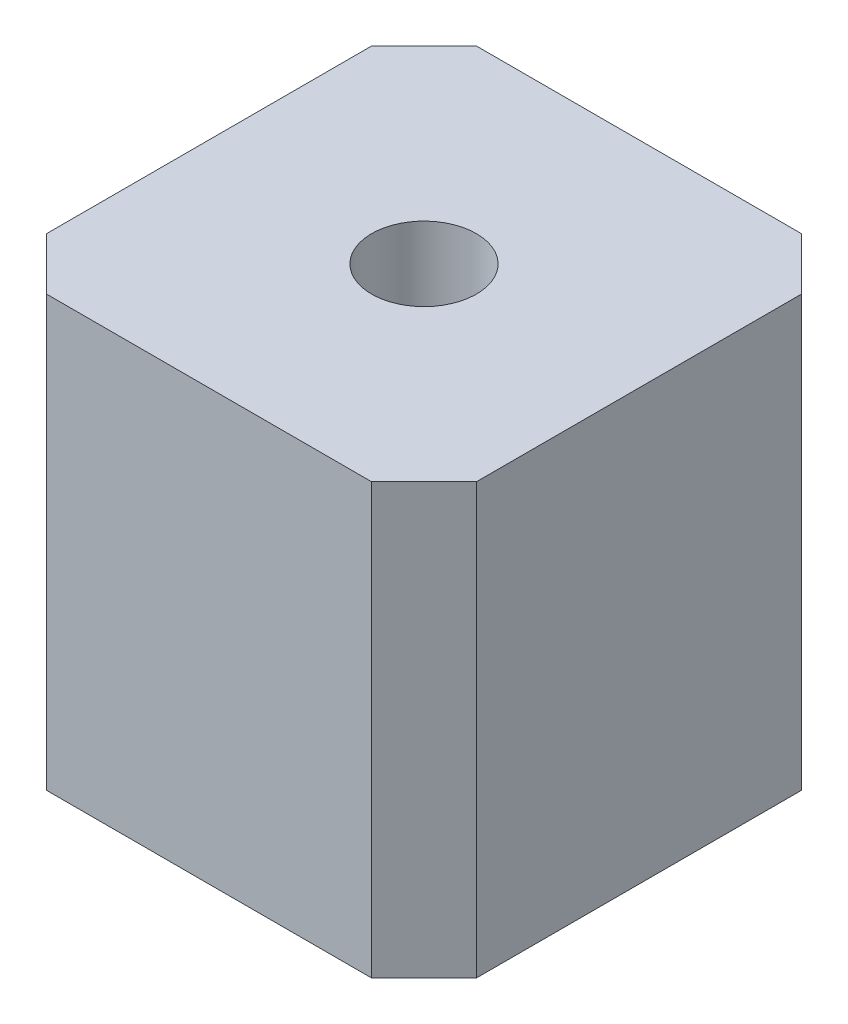
SolidWorks part; units mm, degrees
ref_plane "Front Plane" through (0, 0, 0) normal (0, 0, 1) x (1, 0, 0)
ref_plane "Top Plane" through (0, 0, 0) normal (0, 1, 0) x (1, 0, 0)
ref_plane "Right Plane" through (0, 0, 0) normal (1, 0, 0) x (0, 0, -1)
sketch "Sketch1" plane through (0, 0, 0) normal (0, 1, 0) x (1, 0, 0)
  line L1 (-20.5, -20.5) -> (20.5, -20.5)
  line L2 (-20.5, -20.5) -> (-20.5, 20.5)
  line L3 (-20.5, 20.5) -> (20.5, 20.5)
  line L4 (20.5, -20.5) -> (20.5, 20.5)
  line L5 (-20.5, -20.5) -> (20.5, 20.5) construction
  line L6 (-20.5, 20.5) -> (20.5, -20.5) construction
  point P0 (0, 0)
  dimension "D1" = 41
  dimension "D2" = 41
extrude "Boss-Extrude1" add sketch "Sketch1" along normal blind 41
chamfer "Chamfer1" distance 5 angle 45 4 edges at (20.5, 20.5, 20.5) (20.5, 20.5, -20.5) (-20.5, 20.5, 20.5) (-20.5, 20.5, -20.5)
sketch "Sketch2" plane through (0, 0, 0) normal (0, -1, 0) x (1, 0, 0)
  circle A0 centre (0, 0) radius 5
  dimension "D1" = 10
extrude "Cut-Extrude1" cut sketch "Sketch2" against normal through all
